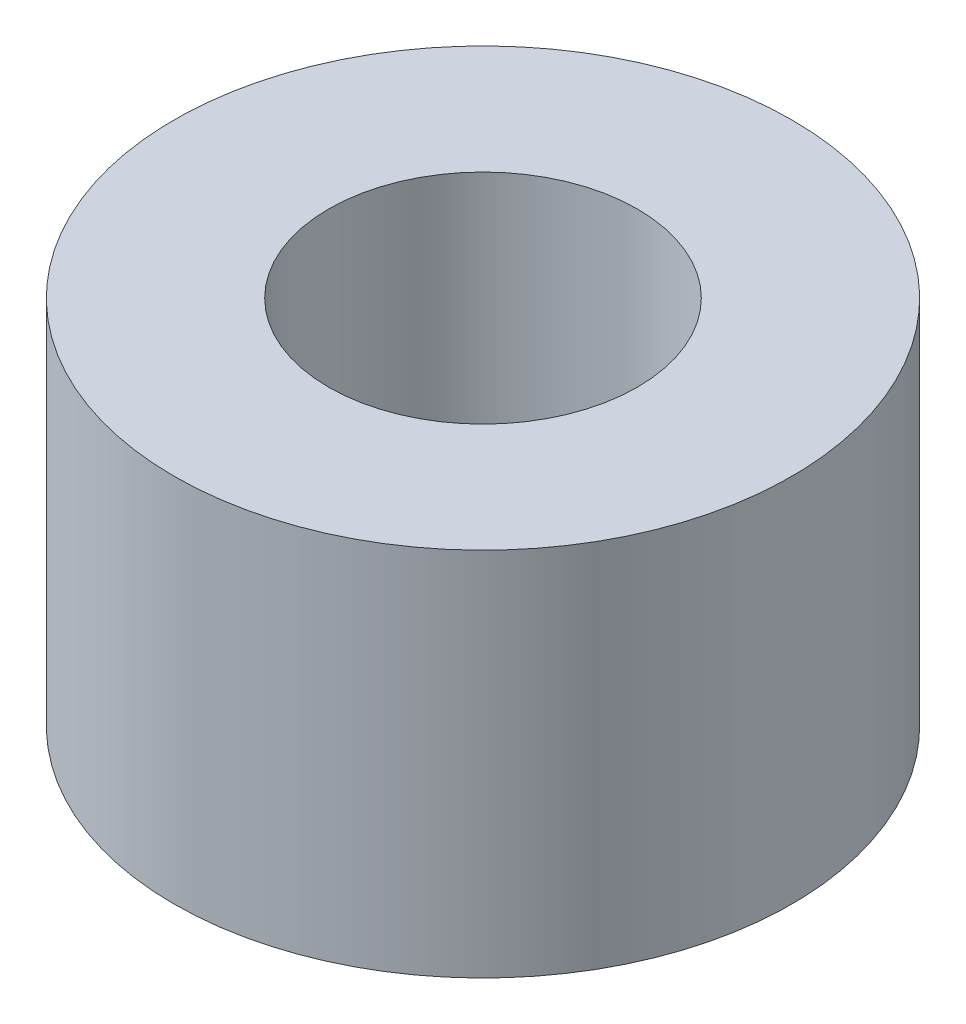
SolidWorks part; units mm, degrees
material "PLA Aero Bambu"
ref_plane "Front Plane" through (0, 0, 0) normal (0, 0, 1) x (1, 0, 0)
ref_plane "Top Plane" through (0, 0, 0) normal (0, 1, 0) x (1, 0, 0)
ref_plane "Right Plane" through (0, 0, 0) normal (1, 0, 0) x (0, 0, -1)
sketch "Sketch1" plane through (0, 0, 0) normal (0, 1, 0) x (1, 0, 0)
  circle A0 centre (0, 0) radius 2.5
  circle A1 centre (0, 0) radius 5
  dimension "D1" = 5
  dimension "D2" = 10
extrude "Boss-Extrude1" add sketch "Sketch1" along normal blind 3 and the other way blind 2
sketch "Sketch2" plane through (0, -2, 0) normal (0, -1, 0) x (1, 0, 0)
  circle A0 centre (0, 0) radius 5
  circle A1 centre (0, 0) radius 5 construction
extrude "Boss-Extrude2" add sketch "Sketch2" along normal blind 1
sketch "Sketch3" plane through (0, -3, 0) normal (0, -1, 0) x (1, 0, 0)
  circle A0 centre (0, 0) radius 1.15
  dimension "D1" = 2.3
extrude "Cut-Extrude1" cut sketch "Sketch3" against normal up to surface (1 mm away) up to face at (0, -2, 2.5)
